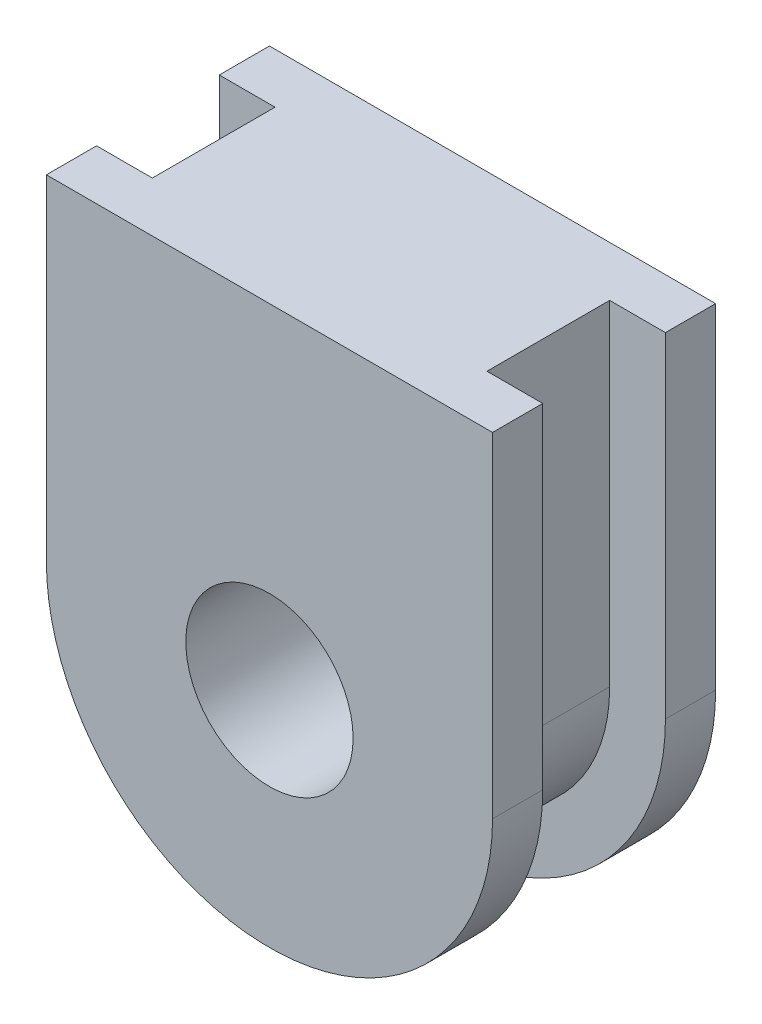
SolidWorks part; units mm, degrees
ref_plane "Vorne" through (0, 0, 0) normal (0, 0, 1) x (1, 0, 0)
ref_plane "Oben" through (0, 0, 0) normal (0, 1, 0) x (1, 0, 0)
ref_plane "Rechts" through (0, 0, 0) normal (1, 0, 0) x (0, 0, -1)
sketch "Skizze1" plane through (0, 0, 0) normal (0, 0, 1) x (1, 0, 0)
  line L1 (-4, 0) -> (4, 0) construction
  line L2 (-4, 0) -> (-4, 6)
  line L3 (-4, 6) -> (4, 6)
  line L4 (4, 0) -> (4, 6)
  arc A0 (-4, 0) -> (4, 0) centre (0, 0) ccw
  circle A1 centre (0, 0) radius 1.5
  dimension "D3" = 3
  dimension "D1" = 8
  dimension "D2" = 10
extrude "Aufsatz-Linear austragen1" add sketch "Skizze1" along normal mid plane 4
sketch "Skizze2" plane through (0, 0, 0) normal (0, 0, 1) x (1, 0, 0)
  line L0 (4, 6) -> (-4, 6) construction
  line L1 (-3, 6) -> (3, 6)
  line L2 (-3, 6) -> (-3, 0)
  line L3 (-3, 0) -> (3, 0) construction
  line L4 (3, 6) -> (3, 0)
  arc A0 (-3, 0) -> (3, 0) centre (0, 0) ccw
  dimension "D1" = 6
extrude "Schnitt-Linear austragen1" cut sketch "Skizze2" against normal mid plane 2.2 flip side to cut
move or copy body "Körper-Verschieben/Kopieren1" [suppressed] bodies to move or copy 104
